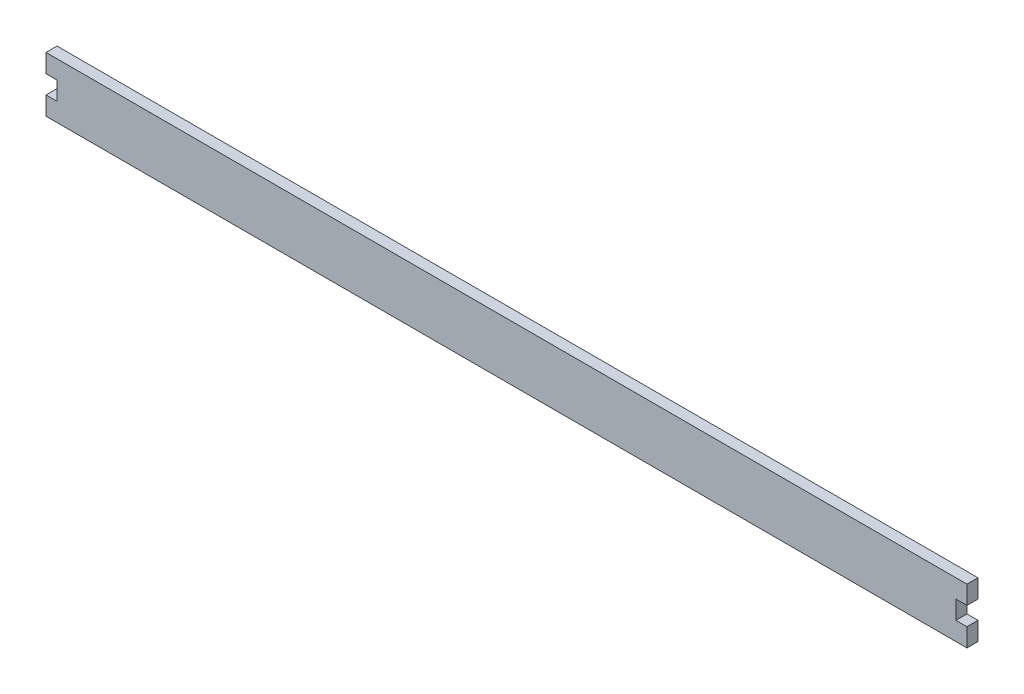
SolidWorks part; units mm, degrees
ref_plane "Alzado" through (0, 0, 0) normal (0, 0, 1) x (1, 0, 0)
ref_plane "Planta" through (0, 0, 0) normal (0, 1, 0) x (1, 0, 0)
ref_plane "Vista lateral" through (0, 0, 0) normal (1, 0, 0) x (0, 0, -1)
sketch "Croquis1" plane through (0, 0, 0) normal (0, 0, 1) x (1, 0, 0)
  line L0 (-71.2047, 23.5511) -> (428.7953, 23.5511)
  line L1 (-71.2047, 23.5511) -> (-71.2047, -6.4489)
  line L2 (-71.2047, -6.4489) -> (428.7953, -6.4489)
  line L3 (428.7953, -6.4489) -> (428.7953, 23.5511)
  line L4 (428.7953, 23.5511) -> (428.7953, 13.5511)
  line L5 (428.7953, 13.5511) -> (422.7953, 13.5511)
  line L6 (422.7953, 13.5511) -> (422.7953, 3.5511)
  line L7 (422.7953, 3.5511) -> (428.7953, 3.5511)
  line L8 (-71.2047, 23.5511) -> (-71.2047, 13.5511)
  line L9 (-71.2047, 13.5511) -> (-65.2047, 13.5511)
  line L10 (-65.2047, 13.5511) -> (-65.2047, 3.5511)
  line L11 (-65.2047, 3.5511) -> (-71.2047, 3.5511)
  dimension "D1" = 500
extrude "Saliente-Extruir1" add sketch "Croquis1" along normal blind 6 contours L10 L11 L1 L2 L3 L7 L6 L5 L0 L9
